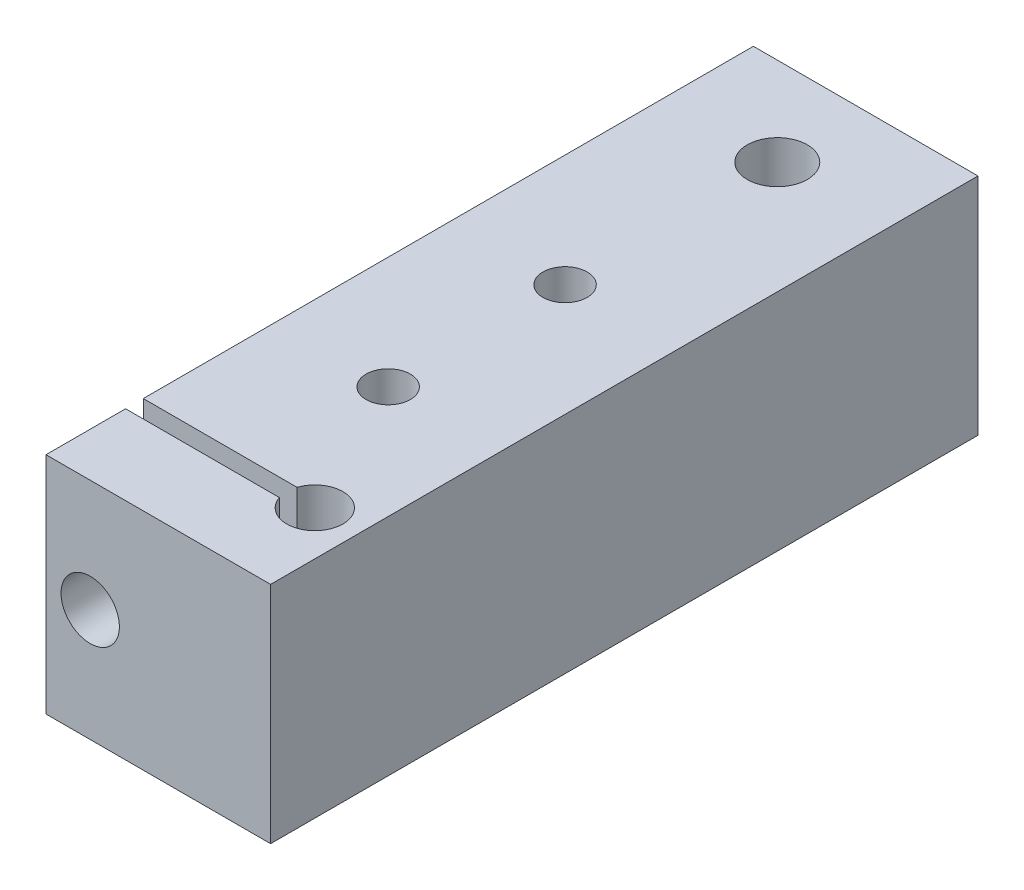
SolidWorks part; units mm, degrees
ref_plane "Front Plane" through (0, 0, 0) normal (0, 0, 1) x (1, 0, 0)
ref_plane "Top Plane" through (0, 0, 0) normal (0, 1, 0) x (1, 0, 0)
ref_plane "Right Plane" through (0, 0, 0) normal (1, 0, 0) x (0, 0, -1)
sketch "Sketch1" plane through (0, 0, 0) normal (0, 1, 0) x (1, 0, 0)
  line L1 (0, 0) -> (25.4, 0)
  line L2 (0, 0) -> (0, 80)
  line L3 (0, 80) -> (25.4, 80)
  line L4 (25.4, 0) -> (25.4, 80)
  dimension "D1" = 25.4
  dimension "D2" = 80
extrude "Boss-Extrude1" add sketch "Sketch1" along normal blind 25.4
hole_wizard "1/4 (0.25) Diameter Hole1" positions "Sketch3" profile "Sketch2" hole size "1/4" standard "ANSI Inch" end condition through all
sketch "Sketch3" plane through (0, 25.4, 0) normal (0, 1, 0) x (1, 0, 0)
  line L0 (0, 0) -> (25.4, 0) construction
  line L1 (25.4, 0) -> (25.4, 80) construction
  point P0 (20.4, 10)
  dimension "D1" = 10
  dimension "D2" = 5
sketch "Sketch2" plane through (20.4, 25.4, -10) normal (1, 0, 0) x (0, 0, 1)
  line L0 (0, 0) -> (0, 25.4)
  line L1 (0, 25.4) -> (3.175, 25.4)
  line L2 (3.175, 25.4) -> (3.175, 0)
  line L5 (3.175, 0) -> (0, 0)
  line L11 (0, -6.35) -> (0, 107.95) construction
  dimension "Thru Hole Dia." = 6.35
  dimension "Thru Hole Depth" = 25.4
sketch "Sketch4" plane through (0, 25.4, 0) normal (0, 1, 0) x (1, 0, 0)
  line L0 (0, 80) -> (0, 0) construction
  line L1 (0, 9) -> (20.4, 9)
  line L2 (0, 9) -> (0, 11)
  line L3 (0, 11) -> (20.4, 11)
  line L4 (20.4, 9) -> (20.4, 11)
  line L5 (0, 9) -> (20.4, 11) construction
  line L6 (0, 11) -> (20.4, 9) construction
  point P0 (10.2, 10)
  dimension "D1" = 2
extrude "Cut-Extrude1" cut sketch "Sketch4" against normal through all
hole_wizard "M6 Clearance Hole1" positions "Sketch6" profile "Sketch5" hole size "M6" standard "ANSI Metric"
sketch "Sketch6" plane through (0, 0, 0) normal (0, 0, 1) x (1, 0, 0)
  line L0 (0, 25.4) -> (0, 0) construction
  point P0 (5, 12.7)
  point P5 (0, 12.7)
  dimension "D1" = 5
sketch "Sketch5" plane through (5, 12.7, 0) normal (1, 0, 0) x (0, -1, 0)
  line L0 (0, 0) -> (0, 10.9818)
  line L1 (0, 10.9818) -> (3.3, 8.999)
  line L2 (3.3, 8.999) -> (3.3, 0)
  line L5 (3.3, 0) -> (0, 0)
  line L10 (0, 10.9818) -> (-3.3, 8.999) construction
  line L11 (0, -6.35) -> (0, 107.95) construction
  dimension "Hole Dia." = 6.6
  dimension "Hole Depth" = 8.999
  dimension "Drill Angle" = 118
hole_wizard "M6x1.0 Tapped Hole1" positions "Sketch8" profile "Sketch7" tap size "M6x1.0" standard "ANSI Metric"
sketch "Sketch8" plane through (0, 0, -11) normal (0, 0, 1) x (1, 0, 0)
  circle A0 centre (5, 12.7) radius 3.3 construction
  point P0 (5, 12.7)
sketch "Sketch7" plane through (5, 12.7, -11) normal (1, 0, 0) x (0, -1, 0)
  line L0 (0, 0) -> (0, 18.5022)
  line L1 (0, 18.5022) -> (2.5, 17)
  line L2 (2.5, 17) -> (2.5, 0)
  line L5 (2.5, 0) -> (0, 0)
  line L10 (0, 18.5022) -> (-2.5, 17) construction
  line L11 (0, -6.35) -> (0, 107.95) construction
  dimension "Tap Drill Dia." = 5
  dimension "Tap Drill Depth" = 17
  dimension "Drill Angle" = 118
cosmetic thread "Hole Thread1"
hole_wizard "M8x1.25 Tapped Hole1" positions "Sketch10" profile "Sketch9" tap size "M8x1.25" standard "ANSI Metric" end condition through all
sketch "Sketch10" plane through (0, 25.4, 0) normal (0, 1, 0) x (1, 0, 0)
  line L0 (25.4, 80) -> (0, 80) construction
  point P0 (12.7, 70)
  point P5 (12.7, 80)
  dimension "D1" = 10
sketch "Sketch9" plane through (12.7, 25.4, -70) normal (1, 0, 0) x (0, 0, 1)
  line L0 (0, 0) -> (0, 25.4)
  line L1 (0, 25.4) -> (3.4, 25.4)
  line L2 (3.4, 25.4) -> (3.4, 0)
  line L5 (3.4, 0) -> (0, 0)
  line L11 (0, -6.35) -> (0, 107.95) construction
  dimension "Thru Tap Drill Dia." = 6.8
  dimension "Thru Tap Drill Depth" = 25.4
cosmetic thread "Hole Thread2"
hole_wizard "M6x1.0 Tapped Hole2" positions "Sketch16" profile "Sketch15" tap size "M6x1.0" standard "ANSI Metric"
sketch "Sketch16" plane through (0, 0, 0) normal (0, -1, 0) x (-1, 0, 0)
  line L0 (-25.4, 80) -> (0, 80) construction
  line L1 (-1.1171, 55) -> (-1.1171, 17) construction
  line L2 (-12.7, 26) -> (-12.7, 46) construction
  line L4 (-1.1171, 55) -> (-1.1171, 17) construction
  line L5 (-1.1171, 55) -> (-1.1171, 17)
  line L6 (-12.7, 36) -> (-1.1171, 36) construction
  point P0 (-12.7, 26)
  point P2 (-12.7, 46)
  point P8 (-12.7, 80)
  dimension "D1" = 20
sketch "Sketch15" plane through (12.7, 0, -26) normal (1, 0, 0) x (0, 0, -1)
  line L0 (0, 0) -> (0, 26.9012)
  line L1 (0, 26.9012) -> (2.5, 25.399)
  line L2 (2.5, 25.399) -> (2.5, 0)
  line L5 (2.5, 0) -> (0, 0)
  line L10 (0, 26.9012) -> (-2.5, 25.399) construction
  line L11 (0, -6.35) -> (0, 107.95) construction
  dimension "Tap Drill Dia." = 5
  dimension "Tap Drill Depth" = 25.399
  dimension "Drill Angle" = 118
cosmetic thread "Hole Thread3"
cosmetic thread "Hole Thread4"
